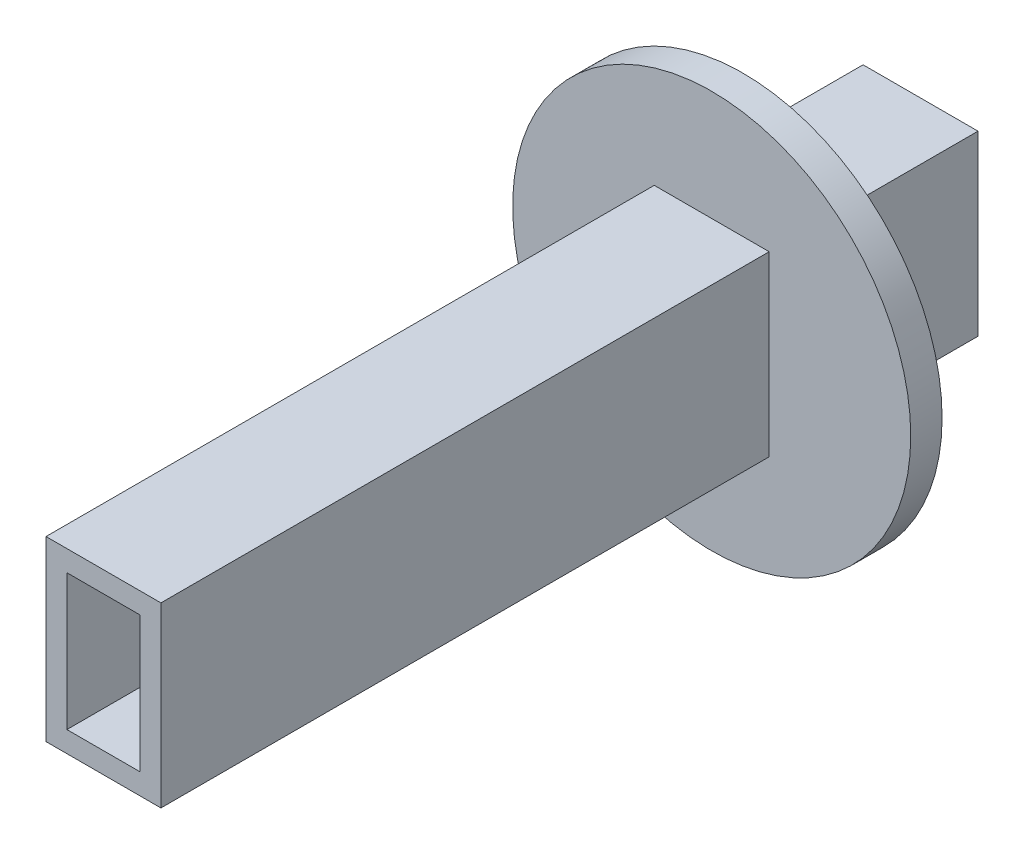
SolidWorks part; units mm, degrees
ref_plane "Front Plane" through (0, 0, 0) normal (0, 0, 1) x (1, 0, 0)
ref_plane "Top Plane" through (0, 0, 0) normal (0, 1, 0) x (1, 0, 0)
ref_plane "Right Plane" through (0, 0, 0) normal (1, 0, 0) x (0, 0, -1)
sketch "Sketch1" plane through (0, 0, 0) normal (0, 0, 1) x (1, 0, 0)
  line L1 (0, 0) -> (7, 0)
  line L2 (0, 0) -> (0, 13)
  line L3 (0, 13) -> (7, 13)
  line L4 (7, 0) -> (7, 13)
  line L5 (-2, -2) -> (9, -2)
  line L6 (-2, -2) -> (-2, 15)
  line L7 (-2, 15) -> (9, 15)
  line L8 (9, -2) -> (9, 15)
  dimension "D1" = 7
  dimension "D2" = 13
  dimension "D3" = 2
  dimension "D4" = 2
  dimension "D5" = 2
  dimension "D6" = 2
extrude "Boss-Extrude1" add sketch "Sketch1" along normal blind 76.2
sketch "Sketch2" plane through (0, 0, 0) normal (0, 0, -1) x (-1, 0, 0)
  line L1 (-9, -2) -> (2, -2)
  line L2 (-9, -2) -> (-9, 15)
  line L3 (-9, 15) -> (2, 15)
  line L4 (2, -2) -> (2, 15)
extrude "Boss-Extrude2" add sketch "Sketch2" along normal blind 2
sketch "Sketch3" plane through (0, -2, 0) normal (0, -1, 0) x (-1, 0, 0)
  line L0 (-9, 2) -> (2, 2) construction
  line L1 (-7, 0) -> (0, 0)
  line L2 (-7, 0) -> (-7, -11)
  line L3 (-7, -11) -> (0, -11)
  line L4 (0, 0) -> (0, -11)
  line L5 (2, -76.2) -> (2, 2) construction
  line L6 (-9, -76.2) -> (-9, 2) construction
  dimension "D1" = 2
  dimension "D2" = 2
  dimension "D3" = 2
  dimension "D4" = 11
extrude "Cut-Extrude1" cut sketch "Sketch3" against normal up to surface (2 mm away) up to face at (3.5, 0, 38.1)
ref_plane "Plane1" through (0, 0, 14.986) normal (0, 0, 1) x (1, 0, 0)
sketch "Sketch4" plane through (0, 0, 14.986) normal (0, 0, 1) x (1, 0, 0)
  line L0 (0, 13) -> (0, 0) construction
  line L2 (-2, 15) -> (9, 15)
  line L3 (-2, 15) -> (-2, -2)
  line L4 (-2, -2) -> (9, -2)
  line L5 (9, 15) -> (9, -2)
  circle A0 centre (3.5, 6.5) radius 19.05
  dimension "D3" = 38.1
  dimension "D1" = 6.5
  dimension "D2" = 3.5
extrude "Boss-Extrude3" add sketch "Sketch4" along normal blind 3
sketch "Sketch5" plane through (0, 0, 14.986) normal (0, 0, -1) x (-1, 0, 0)
  line L1 (-9, 15) -> (2, 15)
  line L2 (-9, 15) -> (-9, -2)
  line L3 (-9, -2) -> (2, -2)
  line L4 (2, 15) -> (2, -2)
  circle A0 centre (-3.5, 6.5) radius 12.7
  dimension "D1" = 25.4
extrude "Boss-Extrude4" add sketch "Sketch5" along normal blind 2.54
